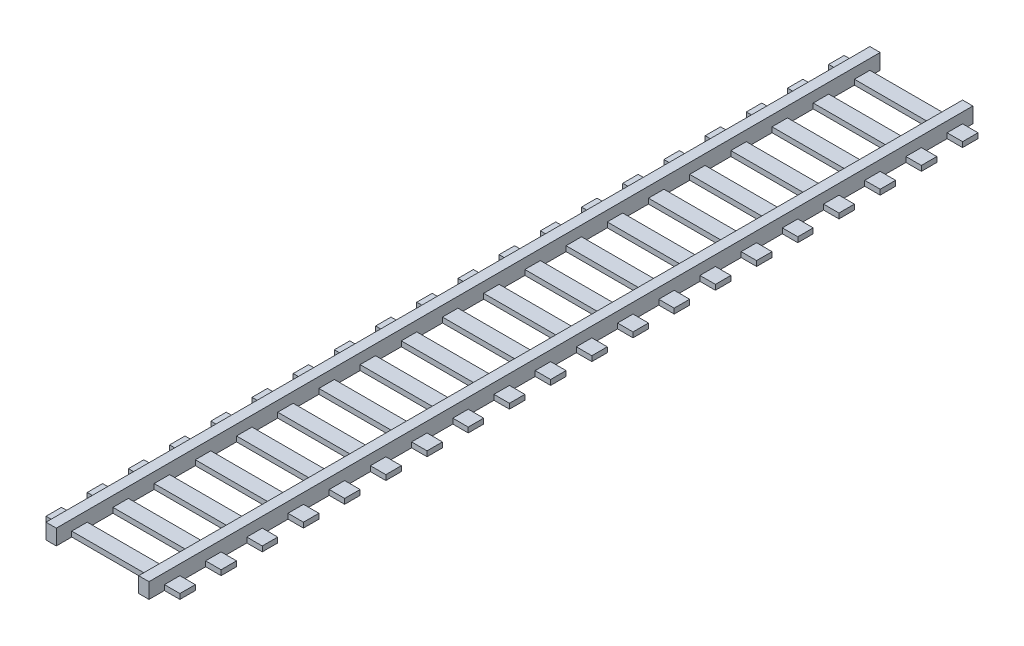
SolidWorks part; units mm, degrees
ref_plane "Front Plane" through (0, 0, 0) normal (0, 0, 1) x (1, 0, 0)
ref_plane "Top Plane" through (0, 0, 0) normal (0, 1, 0) x (1, 0, 0)
ref_plane "Right Plane" through (0, 0, 0) normal (1, 0, 0) x (0, 0, -1)
sketch "Sketch1" plane through (0, 0, 0) normal (0, 1, 0) x (1, 0, 0)
  line L1 (-43.6876, 71.25) -> (-42.6876, 71.25)
  line L2 (-43.6876, 71.25) -> (-43.6876, -88.75)
  line L3 (-43.6876, -88.75) -> (-42.6876, -88.75)
  line L4 (-42.6876, 71.25) -> (-42.6876, -88.75)
  line L5 (-26.6876, 71.25) -> (-25.6876, 71.25)
  line L6 (-26.6876, 71.25) -> (-26.6876, -88.75)
  line L7 (-26.6876, -88.75) -> (-25.6876, -88.75)
  line L8 (-25.6876, 71.25) -> (-25.6876, -88.75)
  dimension "D1" = 160
  dimension "D2" = 1
  dimension "D3" = 1
  dimension "D4" = 16
extrude "Boss-Extrude1" add sketch "Sketch1" along normal blind 3
sketch "Sketch2" plane through (0, 0, 0) normal (0, -1, 0) x (1, 0, 0)
  line L0 (-43.6876, -71.25) -> (-43.6876, 88.75) construction
  line L1 (-43.6876, -71.25) -> (-43.6876, 88.75)
  line L2 (-44.6876, -71.25) -> (-44.6876, 88.75)
  line L3 (-43.6876, -71.25) -> (-44.6876, -71.25)
  line L4 (-43.6876, 88.75) -> (-44.6876, 88.75)
  line L5 (-25.6876, 88.75) -> (-25.6876, -71.25) construction
  line L6 (-25.6876, 88.75) -> (-25.6876, -71.25)
  line L7 (-24.6876, 88.75) -> (-24.6876, -71.25)
  line L8 (-25.6876, 88.75) -> (-24.6876, 88.75)
  line L9 (-25.6876, -71.25) -> (-24.6876, -71.25)
  dimension "D1" = 1
  dimension "D2" = 1
extrude "Boss-Extrude2" add sketch "Sketch2" against normal up to surface (3 mm away) up to face at (-43.1876, 3, 8.75)
sketch "Sketch3" plane through (0, 0, 0) normal (0, -1, 0) x (1, 0, 0)
  line L0 (-44.6876, 88.75) -> (-44.6876, -71.25) construction
  line L1 (-47.6876, 85.75) -> (-21.6876, 85.75)
  line L2 (-47.6876, 85.75) -> (-47.6876, 82.75)
  line L3 (-47.6876, 82.75) -> (-21.6876, 82.75)
  line L4 (-21.6876, 85.75) -> (-21.6876, 82.75)
  line L5 (-24.6876, -71.25) -> (-24.6876, 88.75) construction
  line L6 (-47.6876, 77.75) -> (-47.6876, 74.75)
  line L7 (-47.6876, 77.75) -> (-21.6876, 77.75)
  line L8 (-21.6876, 77.75) -> (-21.6876, 74.75)
  line L9 (-47.6876, 74.75) -> (-21.6876, 74.75)
  line L10 (-47.6876, 69.75) -> (-47.6876, 66.75)
  line L11 (-47.6876, 69.75) -> (-21.6876, 69.75)
  line L12 (-21.6876, 69.75) -> (-21.6876, 66.75)
  line L13 (-47.6876, 66.75) -> (-21.6876, 66.75)
  line L14 (-47.6876, 61.75) -> (-47.6876, 58.75)
  line L15 (-47.6876, 61.75) -> (-21.6876, 61.75)
  line L16 (-21.6876, 61.75) -> (-21.6876, 58.75)
  line L17 (-47.6876, 58.75) -> (-21.6876, 58.75)
  line L18 (-47.6876, 53.75) -> (-47.6876, 50.75)
  line L19 (-47.6876, 53.75) -> (-21.6876, 53.75)
  line L20 (-21.6876, 53.75) -> (-21.6876, 50.75)
  line L21 (-47.6876, 50.75) -> (-21.6876, 50.75)
  line L22 (-47.6876, 45.75) -> (-47.6876, 42.75)
  line L23 (-47.6876, 45.75) -> (-21.6876, 45.75)
  line L24 (-21.6876, 45.75) -> (-21.6876, 42.75)
  line L25 (-47.6876, 42.75) -> (-21.6876, 42.75)
  line L26 (-47.6876, 37.75) -> (-47.6876, 34.75)
  line L27 (-47.6876, 37.75) -> (-21.6876, 37.75)
  line L28 (-21.6876, 37.75) -> (-21.6876, 34.75)
  line L29 (-47.6876, 34.75) -> (-21.6876, 34.75)
  line L30 (-47.6876, 29.75) -> (-47.6876, 26.75)
  line L31 (-47.6876, 29.75) -> (-21.6876, 29.75)
  line L32 (-21.6876, 29.75) -> (-21.6876, 26.75)
  line L33 (-47.6876, 26.75) -> (-21.6876, 26.75)
  line L34 (-47.6876, 21.75) -> (-47.6876, 18.75)
  line L35 (-47.6876, 21.75) -> (-21.6876, 21.75)
  line L36 (-21.6876, 21.75) -> (-21.6876, 18.75)
  line L37 (-47.6876, 18.75) -> (-21.6876, 18.75)
  line L38 (-47.6876, 13.75) -> (-47.6876, 10.75)
  line L39 (-47.6876, 13.75) -> (-21.6876, 13.75)
  line L40 (-21.6876, 13.75) -> (-21.6876, 10.75)
  line L41 (-47.6876, 10.75) -> (-21.6876, 10.75)
  line L42 (-47.6876, 5.75) -> (-47.6876, 2.75)
  line L43 (-47.6876, 5.75) -> (-21.6876, 5.75)
  line L44 (-21.6876, 5.75) -> (-21.6876, 2.75)
  line L45 (-47.6876, 2.75) -> (-21.6876, 2.75)
  line L46 (-47.6876, -2.25) -> (-47.6876, -5.25)
  line L47 (-47.6876, -2.25) -> (-21.6876, -2.25)
  line L48 (-21.6876, -2.25) -> (-21.6876, -5.25)
  line L49 (-47.6876, -5.25) -> (-21.6876, -5.25)
  line L50 (-47.6876, -10.25) -> (-47.6876, -13.25)
  line L51 (-47.6876, -10.25) -> (-21.6876, -10.25)
  line L52 (-21.6876, -10.25) -> (-21.6876, -13.25)
  line L53 (-47.6876, -13.25) -> (-21.6876, -13.25)
  line L54 (-47.6876, -18.25) -> (-47.6876, -21.25)
  line L55 (-47.6876, -18.25) -> (-21.6876, -18.25)
  line L56 (-21.6876, -18.25) -> (-21.6876, -21.25)
  line L57 (-47.6876, -21.25) -> (-21.6876, -21.25)
  line L58 (-47.6876, -26.25) -> (-47.6876, -29.25)
  line L59 (-47.6876, -26.25) -> (-21.6876, -26.25)
  line L60 (-21.6876, -26.25) -> (-21.6876, -29.25)
  line L61 (-47.6876, -29.25) -> (-21.6876, -29.25)
  line L62 (-47.6876, -34.25) -> (-47.6876, -37.25)
  line L63 (-47.6876, -34.25) -> (-21.6876, -34.25)
  line L64 (-21.6876, -34.25) -> (-21.6876, -37.25)
  line L65 (-47.6876, -37.25) -> (-21.6876, -37.25)
  line L66 (-47.6876, -42.25) -> (-47.6876, -45.25)
  line L67 (-47.6876, -42.25) -> (-21.6876, -42.25)
  line L68 (-21.6876, -42.25) -> (-21.6876, -45.25)
  line L69 (-47.6876, -45.25) -> (-21.6876, -45.25)
  line L70 (-47.6876, -50.25) -> (-47.6876, -53.25)
  line L71 (-47.6876, -50.25) -> (-21.6876, -50.25)
  line L72 (-21.6876, -50.25) -> (-21.6876, -53.25)
  line L73 (-47.6876, -53.25) -> (-21.6876, -53.25)
  line L74 (-47.6876, -58.25) -> (-47.6876, -61.25)
  line L75 (-47.6876, -58.25) -> (-21.6876, -58.25)
  line L76 (-21.6876, -58.25) -> (-21.6876, -61.25)
  line L77 (-47.6876, -61.25) -> (-21.6876, -61.25)
  line L78 (-47.6876, -66.25) -> (-47.6876, -69.25)
  line L79 (-47.6876, -66.25) -> (-21.6876, -66.25)
  line L80 (-21.6876, -66.25) -> (-21.6876, -69.25)
  line L81 (-47.6876, -69.25) -> (-21.6876, -69.25)
  dimension "D1" = 3
  dimension "D2" = 3
  dimension "D3" = 3
  dimension "D4" = 3
  dimension "D6" = 3
  dimension "D5" = 20
extrude "Boss-Extrude3" add sketch "Sketch3" against normal blind 1
